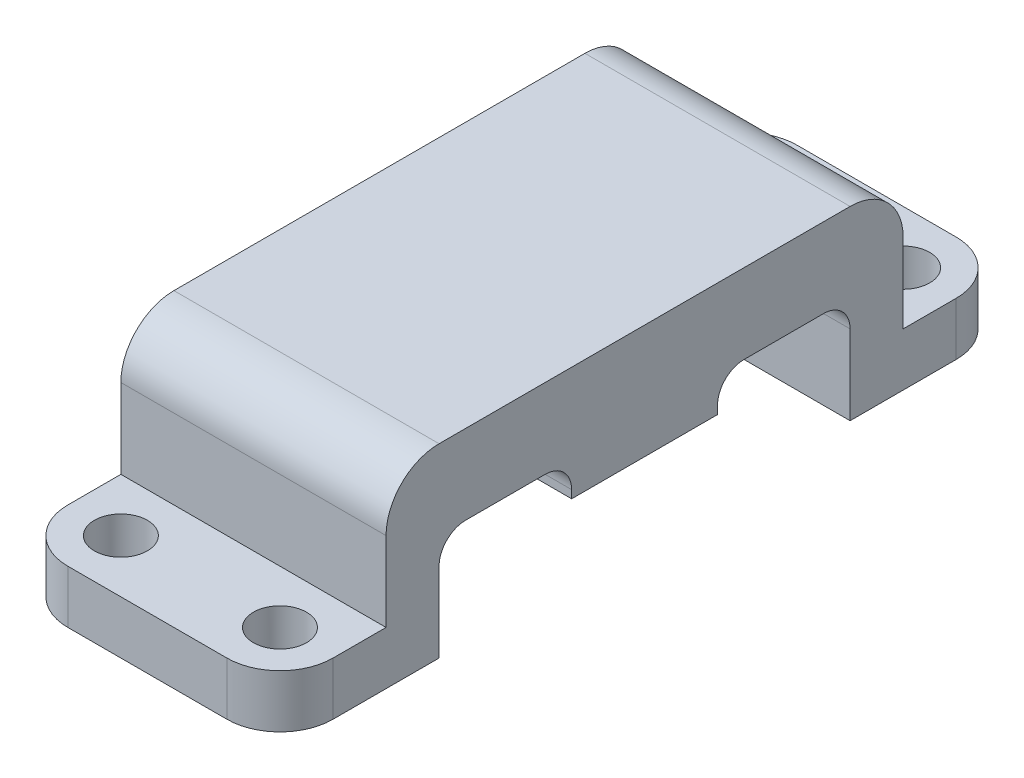
SolidWorks part; units mm, degrees
ref_plane "Front Plane" through (0, 0, 0) normal (0, 0, 1) x (1, 0, 0)
ref_plane "Top Plane" through (0, 0, 0) normal (0, 1, 0) x (1, 0, 0)
ref_plane "Right Plane" through (0, 0, 0) normal (1, 0, 0) x (0, 0, -1)
sketch "Sketch1" plane through (0, 0, 0) normal (1, 0, 0) x (0, 0, -1)
  line L0 (-2.75, 0) -> (-7.75, 0)
  line L1 (-7.75, 0) -> (-7.75, -4)
  line L2 (-7.75, -4) -> (-13.75, -4)
  line L3 (-13.75, -4) -> (-13.75, -2)
  line L4 (-13.75, -2) -> (-9.75, -2)
  line L5 (-9.75, -2) -> (-9.75, 3)
  line L6 (-9.75, 3) -> (9.75, 3)
  line L7 (-2.75, 0) -> (-2.75, -1.3)
  line L8 (-2.75, -1.3) -> (2.75, -1.3)
  line L9 (2.75, 0) -> (2.75, -1.3)
  line L10 (0, 0) -> (0, 3) construction
  line L11 (9.75, -2) -> (9.75, 3)
  line L12 (13.75, -2) -> (9.75, -2)
  line L13 (13.75, -4) -> (13.75, -2)
  line L14 (7.75, -4) -> (13.75, -4)
  line L15 (7.75, 0) -> (7.75, -4)
  line L16 (2.75, 0) -> (7.75, 0)
  point P9 (0, 0)
  point P14 (0, -1.3)
  dimension "D1" = 4
  dimension "D2" = 1.3
  dimension "D3" = 15.5
  dimension "D4" = 3
  dimension "D5" = 2
  dimension "D6" = 4
  dimension "D7" = 2
  dimension "D8" = 5
extrude "Boss-Extrude1" add sketch "Sketch1" along normal blind 10
fillet "Fillet1" radius 2 6 edges at (0, -3, -13.75) (10, -3, -13.75) (0, -3, 13.75) (10, -3, 13.75) (5, 3, -9.75) (5, 3, 9.75)
sketch "Sketch2" plane through (0, -2, 0) normal (0, 1, 0) x (1, 0, 0)
  line L0 (8, -13.75) -> (8, -9.75) construction
  line L1 (10, -9.75) -> (0, -9.75) construction
  line L2 (0, 0) -> (10, 0) construction
  line L3 (10, 7.75) -> (10, -7.75) construction
  circle A0 centre (8, -11.75) radius 1
  circle A1 centre (2, -11.75) radius 1
  arc A2 (0, -11.75) -> (2, -13.75) centre (2, -11.75) ccw construction
  circle A3 centre (2, 11.75) radius 1
  circle A4 centre (8, 11.75) radius 1
  dimension "D1" = 2
extrude "Cut-Extrude1" cut sketch "Sketch2" against normal through all both and the other way through all
fillet "Fillet2" radius 1 4 edges at (5, 0, -7.75) (5, 0, -2.75) (5, 0, 2.75) (5, 0, 7.75)
